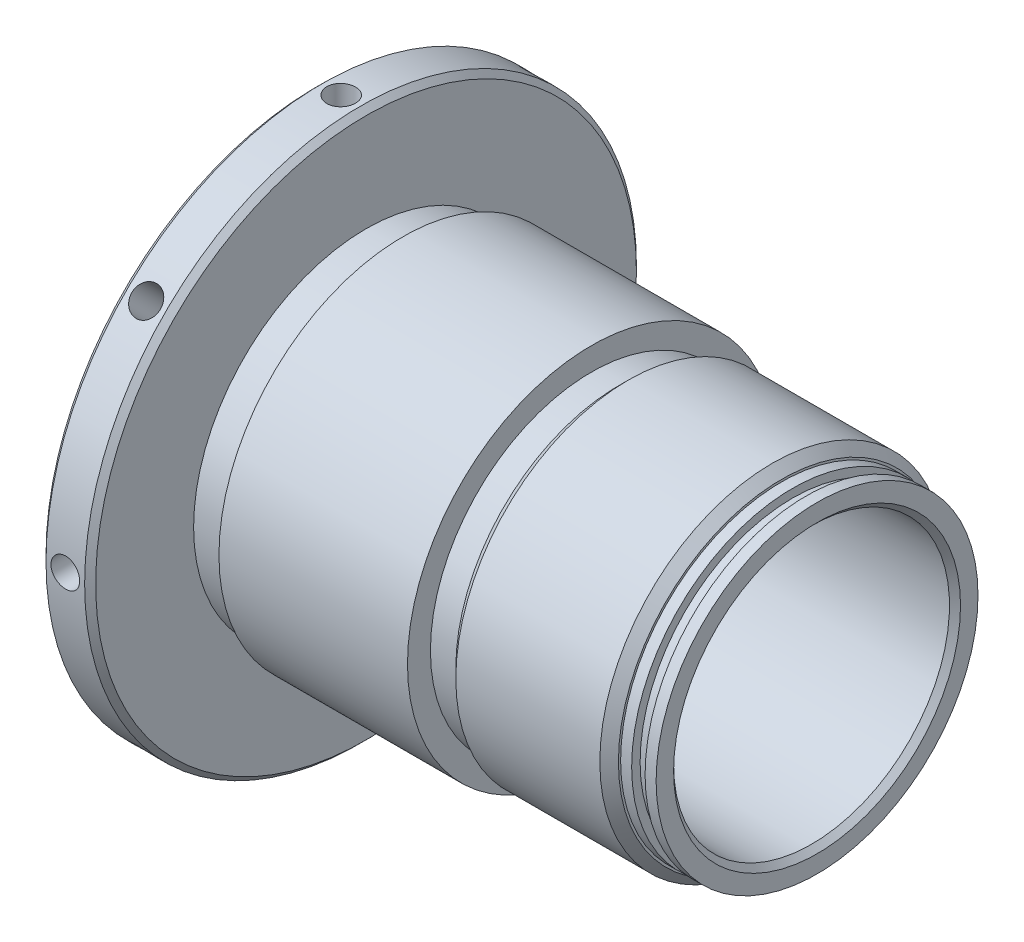
SolidWorks part; units mm, degrees
material "AISI 440C PER AMS 5630"
ref_plane "XY" through (0, 0, 0) normal (0, 0, 1) x (1, 0, 0)
ref_plane "XZ" through (0, 0, 0) normal (0, 1, 0) x (1, 0, 0)
ref_plane "YZ" through (0, 0, 0) normal (1, 0, 0) x (0, 0, -1)
sketch "Sketch1" plane through (0, 0, 0) normal (0, 0, 1) x (1, 0, 0)
  line L0 (0, 0) -> (105.4936, 0) construction
  line L1 (0, 19.558) -> (0, 25.3937)
  line L3 (19.304, 20.32) -> (19.304, 14.2311) construction
  line L4 (0, 25.3937) -> (62.2808, 25.3937)
  line L5 (17.78, 20.32) -> (20.828, 20.32)
  line L6 (62.2808, 19.05) -> (22.098, 19.05)
  line L8 (17.018, 19.558) -> (0, 19.558)
  line L9 (20.828, 20.32) -> (22.098, 19.05)
  line L10 (17.78, 20.32) -> (17.018, 19.558)
  line L12 (62.2808, 25.3937) -> (62.2808, 19.05)
  point P8 (25.908, 19.05)
  point P18 (12.7, 19.558)
  dimension "D2" = 3.048
  dimension "D8" = 135
  dimension "D12" = 6.604
  dimension "D5" = 0.762
  dimension "D1" = 38.1
  dimension "D3" = 39.116
  dimension "D4" = 19.304
  dimension "D6" = 62.2808
  dimension "D7" = 50.7873
  dimension "D11" = 13.208
  dimension "D13" = 135
revolve "Revolve1" add sketch "Sketch1" angle 360 about L0
sketch "Sketch2" plane through (0, 0, 0) normal (0, 0, 1) x (1, 0, 0)
  line L0 (62.2808, 25.3937) -> (0, 25.3937) construction
  line L1 (31.115, 25.3937) -> (62.2808, 25.3937)
  line L2 (31.115, 25.3937) -> (31.115, 22.225)
  line L3 (34.925, 23.8125) -> (57.3786, 23.8125)
  line L4 (62.2808, 25.3937) -> (62.2808, 22.225)
  line L5 (62.2808, -25.3937) -> (62.2808, 25.3937) construction
  line L6 (0, 0) -> (36.2503, 0) construction
  line L7 (2.8458, 22.5298) -> (34.9432, 22.5298) construction
  line L8 (34.925, 22.225) -> (34.925, 23.8125)
  line L9 (31.115, 22.225) -> (34.925, 22.225)
  line L10 (60.7568, 22.225) -> (62.2808, 22.225)
  line L12 (58.9026, 22.225) -> (58.9026, 21.0566)
  line L13 (58.9026, 21.0566) -> (60.7568, 21.0566)
  line L14 (60.7568, 22.225) -> (60.7568, 21.0566)
  line L16 (57.3786, 23.8125) -> (57.3786, 22.225)
  line L17 (57.3786, 22.225) -> (58.9026, 22.225)
  dimension "D3" = 44.45
  dimension "D1" = 5.207
  dimension "D2" = 47.625
  dimension "D4" = 45.0596
  dimension "D5" = 3.81
  dimension "D6" = 42.1132
  dimension "D7" = 1.524
  dimension "D8" = 1.8542
  dimension "D9" = 1.524
revolve "Cut-Revolve1" cut sketch "Sketch2" angle 360 about L6
cosmetic thread "Cosmetic Thread1" parameters "D2"=45.0596
ref_plane "Plane1" through (25.908, 0, 0) normal (1, 0, 0) x (0, 0, -1)
chamfer "Chamfer1" distance 0.762 angle 45 1 edges at (62.2808, 0, 19.05)
sketch "Sketch3" plane through (0, 0, 0) normal (0, 0, 1) x (1, 0, 0)
  line L0 (0, 0) -> (-41.4207, 0) construction
  line L1 (17.018, 19.558) -> (0, 19.558) construction
  line L2 (0, 19.558) -> (-6.858, 19.558)
  line L3 (0, 19.558) -> (0, 38.1)
  line L4 (0, 38.1) -> (-6.858, 38.1)
  line L5 (-6.858, 19.558) -> (-6.858, 38.1)
  line L6 (0, 25.3937) -> (0, -25.3937) construction
  dimension "D1" = 6.858
  dimension "D2" = 76.2
revolve "Revolve2" add sketch "Sketch3" angle 360 about L0
sketch "Sketch5" plane through (0, 0, 0) normal (0, 0, 1) x (1, 0, 0)
  line L0 (31.115, 25.3937) -> (0, 25.3937) construction
  line L1 (5.08, 25.3937) -> (0, 25.3937)
  line L2 (5.08, 25.3937) -> (5.08, 23.8125)
  line L3 (5.08, 23.8125) -> (0, 23.8125)
  line L4 (0, 25.3937) -> (0, 23.8125)
  line L5 (0, -38.1) -> (0, 38.1) construction
  line L6 (23.3533, 0) -> (53.789, 0) construction
  line L7 (0, 0) -> (105.4936, 0) construction
  dimension "D1" = 5.08
  dimension "D2" = 47.625
revolve "Cut-Revolve2" cut sketch "Sketch5" angle 360 about L6
chamfer "Chamfer3" distance 0.762 angle 45 2 edges at (0, 0, -38.1) (-6.858, 0, -38.1)
ref_plane "Plane2" through (-3.429, 38.1, 0) normal (0, 1, 0) x (0, 0, 1)
sketch "Sketch6" plane through (-3.429, 38.1, 0) normal (0, 1, 0) x (0, 0, 1)
  line L0 (0, 0) -> (12.4962, 0) construction
  line L1 (37.338, 3.429) -> (-37.338, 3.429) construction
  line L2 (-19.558, -3.429) -> (19.558, -3.429) construction
  line L3 (0, 3.429) -> (0, 108.9226) construction
  circle A0 centre (0, 0) radius 1.9812
  dimension "D1" = 3.9624
extrude "Cut-Extrude2" cut sketch "Sketch6" against normal blind 6.35
chamfer "Chamfer4" distance 1.2827 angle 45 2 edges at (34.925, 0, 23.8125) (57.3786, 0, 23.8125)
pattern_circular "CirPattern2" count 8 every 45 about axis through (0, 0, 0) along (1, 0, 0) of "Cut-Extrude2"
sketch "Sketch7" plane through (-6.858, 0, 0) normal (-1, 0, 0) x (0, 0, 1)
  line L0 (-11.1071, 26.3063) -> (11.1071, 26.3063) construction
  line L1 (0, 26.3063) -> (0, 0) construction
  text T0 "STG 0-1"
extrude "Extrude1" cut sketch "Sketch7" against normal blind 0.0254
